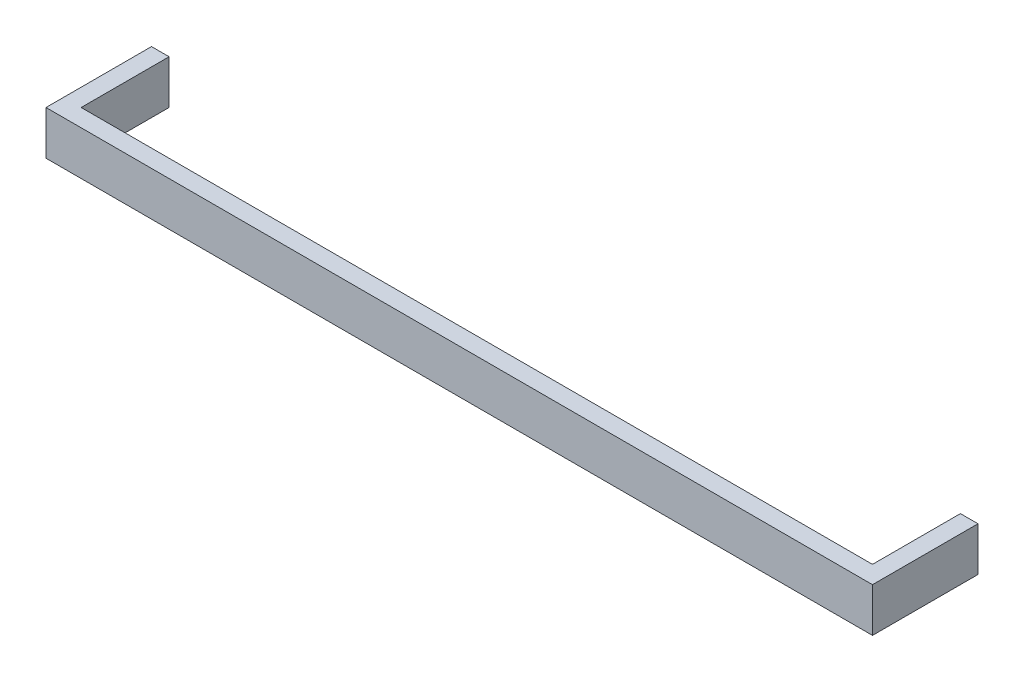
SolidWorks part; units mm, degrees
ref_plane "Front Plane" through (0, 0, 0) normal (0, 0, 1) x (1, 0, 0)
ref_plane "Top Plane" through (0, 0, 0) normal (0, 1, 0) x (1, 0, 0)
ref_plane "Right Plane" through (0, 0, 0) normal (1, 0, 0) x (0, 0, -1)
sketch "Sketch1" plane through (0, 0, 0) normal (0, 1, 0) x (1, 0, 0)
  line L0 (0, 0) -> (90, 0)
  line L1 (90, 0) -> (90, 10)
  line L2 (90, 10) -> (92, 10)
  line L3 (92, 10) -> (92, -2)
  line L4 (92, -2) -> (-2, -2)
  line L5 (-2, -2) -> (-2, 10)
  line L6 (-2, 10) -> (0, 10)
  line L7 (0, 10) -> (0, 0)
extrude "Boss-Extrude1" add sketch "Sketch1" along normal blind 5
